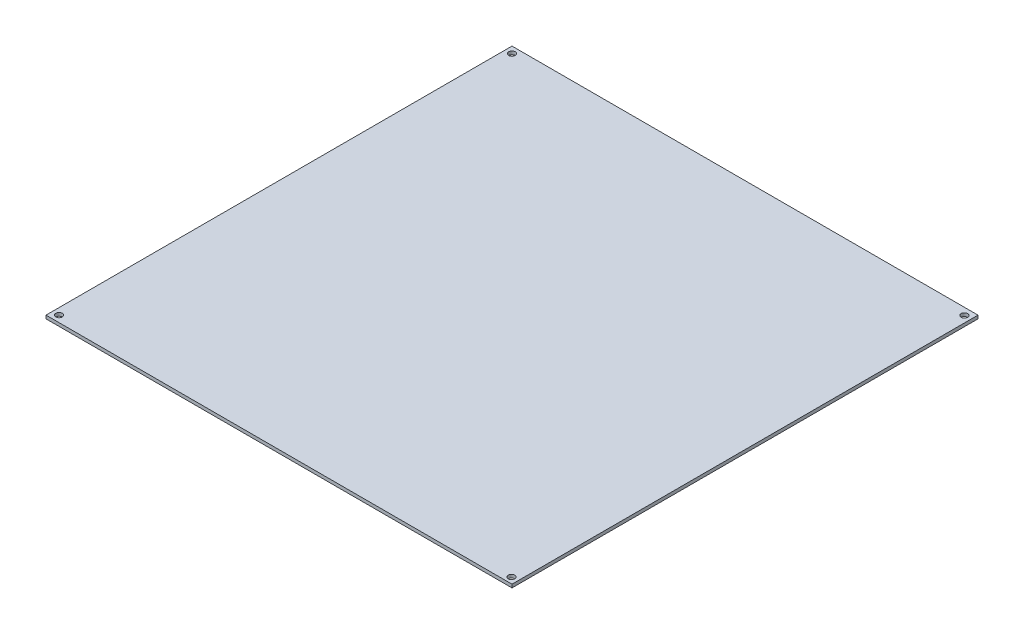
SolidWorks part; units mm, degrees
material "Liga 1060"
ref_plane "Alzado" through (0, 0, 0) normal (0, 0, 1) x (1, 0, 0)
ref_plane "Planta" through (0, 0, 0) normal (0, 1, 0) x (1, 0, 0)
ref_plane "Vista lateral" through (0, 0, 0) normal (1, 0, 0) x (0, 0, -1)
sketch "Croquis1" plane through (0, 0, 0) normal (0, 1, 0) x (1, 0, 0)
  line L1 (-125.0431, 61.6824) -> (88.9569, 61.6824)
  line L2 (-125.0431, 61.6824) -> (-125.0431, -152.3176)
  line L3 (-125.0431, -152.3176) -> (88.9569, -152.3176)
  line L4 (88.9569, 61.6824) -> (88.9569, -152.3176)
  circle A0 centre (-122.043, 58.6824) radius 1.5
  circle A1 centre (85.9569, 58.4324) radius 1.5
  circle A2 centre (-122.043, -149.3176) radius 1.5
  circle A3 centre (85.9569, -149.5676) radius 1.5
  dimension "D2" = 3
  dimension "D3" = 208
  dimension "D4" = 208
  dimension "D5" = 208
  dimension "D6" = 208
  dimension "D7" = 3
  dimension "D8" = 3
  dimension "D9" = 3
  dimension "D1" = 214
extrude "Saliente-Extruir2" add sketch "Croquis1" along normal blind 1.5
